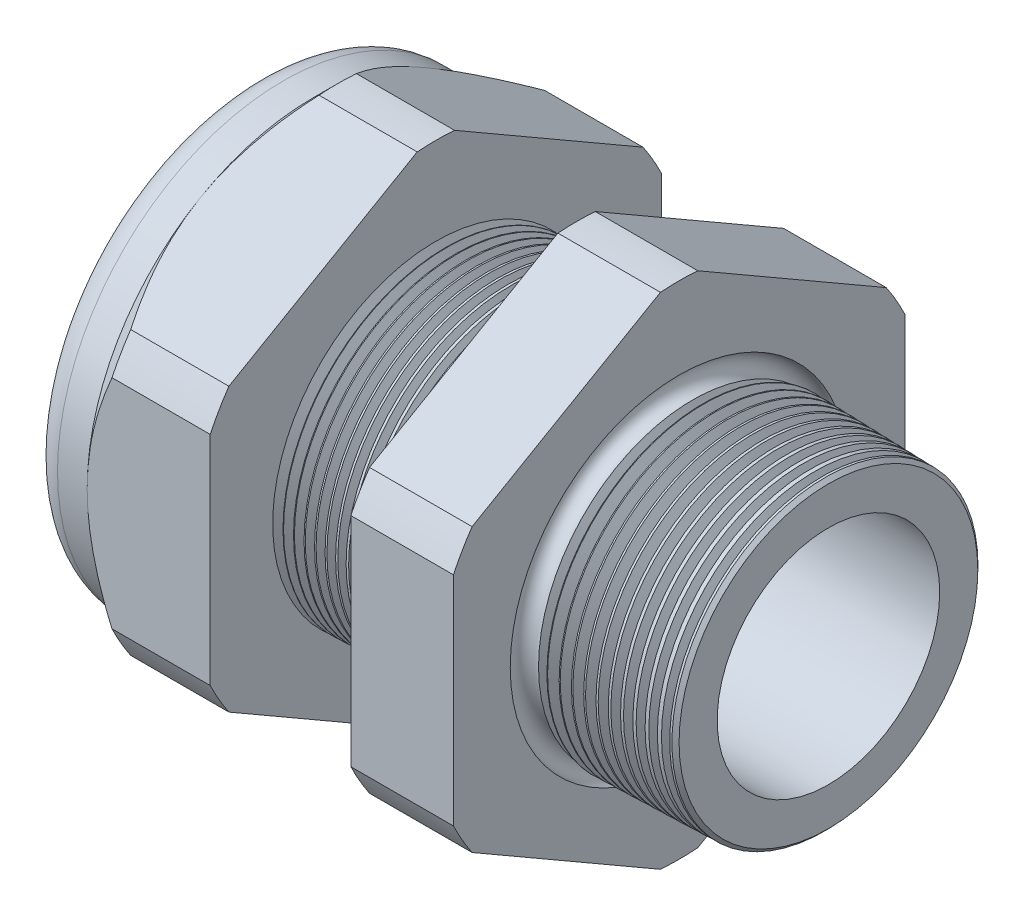
SolidWorks part; units mm, degrees
ref_plane "Front Plane" through (0, 0, 0) normal (0, 0, 1) x (1, 0, 0)
ref_plane "Top Plane" through (0, 0, 0) normal (0, 1, 0) x (1, 0, 0)
ref_plane "Right Plane" through (0, 0, 0) normal (1, 0, 0) x (0, 0, -1)
sketch "Sketch10" plane through (0, 0, 0) normal (0, 0, 1) x (1, 0, 0)
  line L0 (0, 0) -> (-115.3565, 0) construction
  line L1 (-38.862, 9.017) -> (-25.662, 9.017)
  line L2 (3.048, 8.1382) -> (3.048, 11.1862)
  line L3 (-7.874, 11.4722) -> (3.048, 11.1862)
  line L4 (-7.874, 33.02) -> (-7.874, 11.4722)
  line L5 (-7.874, 33.02) -> (-15.374, 33.02)
  line L6 (-15.374, 33.02) -> (-15.374, 11.6686)
  line L7 (-25.662, 11.938) -> (-15.374, 11.6686)
  line L8 (-25.662, 11.938) -> (-25.662, 33.02)
  line L9 (-25.662, 33.02) -> (-34.662, 33.02)
  line L10 (-34.662, 33.02) -> (-34.662, 16.51)
  line L11 (-34.662, 16.51) -> (-38.862, 16.51)
  line L12 (-38.862, 16.51) -> (-38.862, 9.017)
  line L13 (-25.662, 9.017) -> (3.048, 8.1382)
  dimension "D1" = 41.91
  dimension "D2" = 18.034
  dimension "D3" = 1.5
  dimension "D4" = 3.048
  dimension "A" = 23.876
  dimension "D6" = 33.02
  dimension "D8" = 66.04
  dimension "D9" = 4.2
  dimension "D10" = 9
  dimension "D11" = 7.5
  dimension "D" = 10.922
revolve "Revolve2" add sketch "Sketch10" angle 360 about L0
sketch "Sketch12" plane through (-34.662, 0, 0) normal (-1, 0, 0) x (0, 0, 1)
  line L1 (-1.3666, 18.2751) -> (-15.1434, 10.3211)
  line L2 (-16.51, 7.954) -> (-16.51, -7.954)
  line L3 (-15.1434, -10.3211) -> (-1.3666, -18.2751)
  line L4 (1.3666, -18.2751) -> (15.1434, -10.3211)
  line L5 (16.51, -7.954) -> (16.51, 7.954)
  line L6 (15.1434, 10.3211) -> (1.3666, 18.2751)
  circle A0 centre (0, 0) radius 16.51 construction
  arc A1 (1.3666, 18.2751) -> (-1.3666, 18.2751) centre (0, 0) ccw
  arc A2 (-15.1434, 10.3211) -> (-16.51, 7.954) centre (0, 0) ccw
  arc A3 (-16.51, -7.954) -> (-15.1434, -10.3211) centre (0, 0) ccw
  arc A4 (-1.3666, -18.2751) -> (1.3666, -18.2751) centre (0, 0) ccw
  arc A5 (15.1434, -10.3211) -> (16.51, -7.954) centre (0, 0) ccw
  arc A6 (16.51, 7.954) -> (15.1434, 10.3211) centre (0, 0) ccw
  dimension "D2" = 36.6522
  dimension "D1" = 33.02
extrude "Cut-Extrude2" cut sketch "Sketch12" against normal through all flip side to cut
fillet "Fillet4" radius 2.032 1 edges at (-38.862, 0, -16.51)
sketch "Sketch19" plane through (-34.662, 0, 0) normal (-1, 0, 0) x (0, 0, 1)
  line L0 (16.51, 0) -> (16.51, 7.954) construction
  circle A0 centre (0, 0) radius 16.51
extrude "Cut-Extrude3" cut sketch "Sketch19" against normal blind 3.998 draft 45 flip side to cut
chamfer "Chamfer1" distance 0.254 angle 45 1 edges at (3.048, 0, -11.1862)
sketch "Sketch21" plane through (-38.862, 0, 0) normal (-1, 0, 0) x (0, 0, 1)
  circle A0 centre (0, 0) radius 9.017
  circle A2 centre (0, 0) radius 9.017 construction
extrude "plug" add sketch "Sketch21" against normal blind 8.89 separate body
sketch "Sketch22" plane through (-38.862, 0, 0) normal (-1, 0, 0) x (0, 0, 1)
  circle A0 centre (0, 0) radius 8.763
  circle A1 centre (0, 0) radius 9.017 construction
  dimension "D1" = 0.254
extrude "Cut-Extrude4" cut sketch "Sketch22" against normal blind 0.508
sketch "Sketch27" plane through (-38.354, 0, 0) normal (-1, 0, 0) x (0, 0, 1)
  line L0 (-4.3624, 0) -> (4.3624, 0) construction
  circle A0 centre (-5.0653, 0) radius 3.683
  circle A1 centre (0, 0) radius 8.763 construction
  dimension "D1" = 0.0147
  dimension "holedia" = 7.366
extrude "plugholes" cut sketch "Sketch27" against normal through all
pattern_circular "CirPattern1" count 2 over 360 about axis through (0, 0, 0) along (1, 0, 0) of "plugholes"
sketch "Sketch28" [suppressed] plane through (-29.464, 0, 0) normal (-1, 0, 0) x (0, 0, 1)
  circle A0 centre (0, 0) radius 0.762
  dimension "midholedia" = 7.366
extrude "midhole" [suppressed] cut sketch "Sketch28" against normal through all
sketch "Sketch29" plane through (0, 0, 0) normal (0, 0, 1) x (1, 0, 0)
  line L0 (-25.662, 11.938) -> (-24.929, 11.9188)
  line L1 (-15.374, 11.6686) -> (-25.662, 11.938) construction
  line L2 (-24.929, 11.9188) -> (-25.3121, 11.2936)
  line L3 (-25.3121, 11.2936) -> (-25.662, 11.938)
  dimension "D1" = 60
  dimension "D2" = 60
  dimension "D3" = 0.635
revolve "Cut-Revolve1" cut sketch "Sketch29" angle 360 about axis through (0, 0, 0) along (-1, 0, 0)
pattern_linear "LPattern1" count 14 spacing 0.762 along (1, 0, 0) of "Cut-Revolve1"
sketch "Sketch30" plane through (0, 0, 0) normal (0, 0, 1) x (1, 0, 0)
  line L0 (-7.874, 11.4722) -> (-6.9944, 11.4492)
  line L1 (-7.874, 18.2751) -> (-7.874, 10.3211) construction
  line L2 (2.7941, 11.1929) -> (-7.874, 11.4722) construction
  line L3 (-6.9944, 11.4492) -> (-7.4542, 10.6989)
  line L4 (-7.4542, 10.6989) -> (-7.874, 11.4722)
  dimension "D1" = 60
  dimension "D2" = 60
  dimension "D3" = 0.762
revolve "Cut-Revolve2" cut sketch "Sketch30" angle 360 about axis through (0, 0, 0) along (-1, 0, 0)
pattern_linear "LPattern2" count 12 spacing 0.889 along (1, 0, 0) of "Cut-Revolve2"
sketch "Sketch31" [suppressed] plane through (-38.354, 0, 0) normal (-1, 0, 0) x (0, 0, 1)
  line L0 (-1.905, 1.905) -> (1.905, 1.905)
  line L1 (-1.905, -1.905) -> (1.905, -1.905)
  circle A0 centre (0, 0) radius 1.905 construction
  arc A1 (-1.905, 1.905) -> (-1.905, -1.905) centre (-1.905, 0) ccw
  arc A2 (1.905, 1.905) -> (1.905, -1.905) centre (1.905, 0) cw
extrude "Cut-Extrude5" [suppressed] cut sketch "Sketch31" against normal through all
sketch "Sketch32" plane through (0, 0, 0) normal (0, 0, 1) x (1, 0, 0)
  line L0 (-7.874, 18.2751) -> (-7.874, 10.3211) construction
  circle A0 centre (-7.747, 11.4722) radius 0.889
  dimension "D2" = 1.778
  dimension "D1" = 0.127
revolve "Cut-Revolve3" cut sketch "Sketch32" angle 360 about axis through (0, 0, 0) along (-1, 0, 0)
